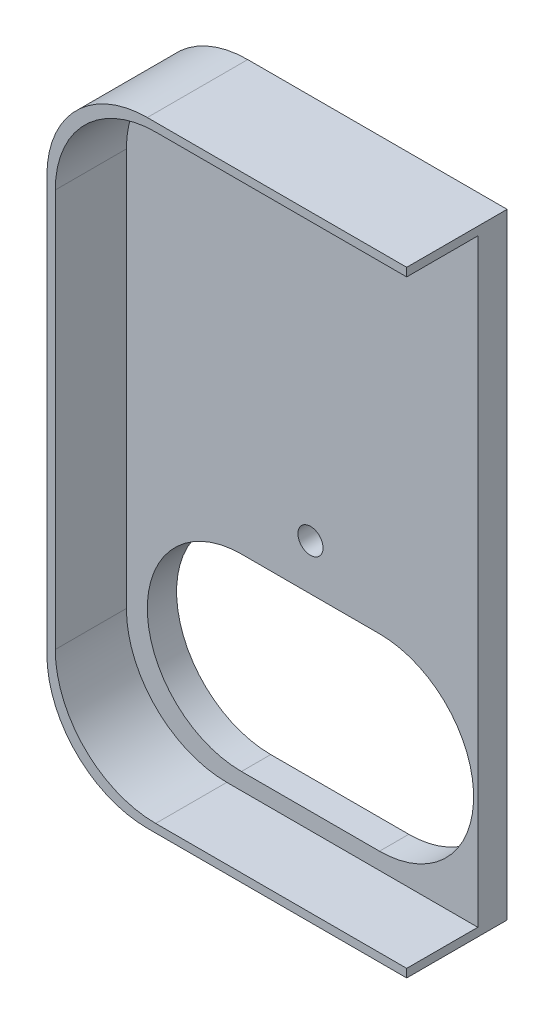
SolidWorks part; units mm, degrees
ref_plane "Front Plane" through (0, 0, 0) normal (1, 0, 0) x (0, 1, 0)
ref_plane "Top Plane" through (0, 0, 0) normal (0, 0, 1) x (0, 1, 0)
ref_plane "Right Plane" through (0, 0, 0) normal (0, 1, 0) x (-1, 0, 0)
sketch "Sketch2" plane through (0, 0, 0) normal (0, 0, 1) x (0, 1, 0)
  line L1 (-36.78, -21.5) -> (36.78, -21.5)
  line L2 (-36.78, -21.5) -> (-36.78, 9.5)
  line L3 (-24.78, 21.5) -> (24.78, 21.5)
  line L4 (36.78, -21.5) -> (36.78, 9.5)
  line L5 (-36.78, -21.5) -> (36.78, 21.5) construction
  line L6 (-36.78, 21.5) -> (36.78, -21.5) construction
  arc A0 (24.78, 21.5) -> (36.78, 9.5) centre (24.78, 9.5) cw
  arc A1 (-24.78, 21.5) -> (-36.78, 9.5) centre (-24.78, 9.5) ccw
  point P1 (0, 0)
  dimension "D5" = 12
  dimension "D1" = 73.56
  dimension "D2" = 43
extrude "Boss-Extrude2" add sketch "Sketch2" along normal blind 12
sketch "Sketch5" plane through (0, 0, 12) normal (0, 0, 1) x (1, 0, 0)
  line L0 (21.5, -36.78) -> (21.5, 36.78) construction
  line L1 (21.5, -35.78) -> (-8.5, -35.78)
  line L2 (21.5, -35.78) -> (21.5, 35.78)
  line L3 (21.5, 35.78) -> (-8.5, 35.78)
  line L4 (-20.5, -23.78) -> (-20.5, 23.78)
  line L5 (21.5, 36.78) -> (-9.5, 36.78) construction
  line L6 (21.5, -36.78) -> (-9.5, -36.78) construction
  line L7 (-21.5, -24.78) -> (-21.5, 24.78) construction
  arc A0 (-8.5, -35.78) -> (-20.5, -23.78) centre (-8.5, -23.78) cw
  arc A1 (-8.5, 35.78) -> (-20.5, 23.78) centre (-8.5, 23.78) ccw
  dimension "D4" = 12
  dimension "D1" = 1
  dimension "D2" = 1
  dimension "D3" = 1
extrude "Cut-Extrude1" cut sketch "Sketch5" against normal blind 8.5
sketch "Sketch6" plane through (0, 0, 3.5) normal (0, 0, 1) x (1, 0, 0)
  line L1 (9.75, -33.78) -> (-6.75, -33.78)
  line L3 (9.75, -11.28) -> (-6.75, -11.28)
  line L5 (-8.5, -35.78) -> (21.5, -35.78) construction
  line L6 (-20.5, 23.78) -> (-20.5, -23.78) construction
  line L7 (-18, -22.53) -> (21, -22.53) construction
  arc A0 (-6.75, -33.78) -> (-6.75, -11.28) centre (-6.75, -22.53) cw
  arc A1 (9.75, -11.28) -> (9.75, -33.78) centre (9.75, -22.53) cw
  circle A2 centre (1.5, -5.78) radius 1.5
  point P6 (-18, -22.53)
  point P7 (21, -22.53)
  point P14 (1.5, -5.78)
  dimension "D1" = 39
  dimension "D2" = 22.5
  dimension "D3" = 2
  dimension "D4" = 2.5
  dimension "D5" = 30
extrude "Cut-Extrude2" cut sketch "Sketch6" against normal blind 8.5
